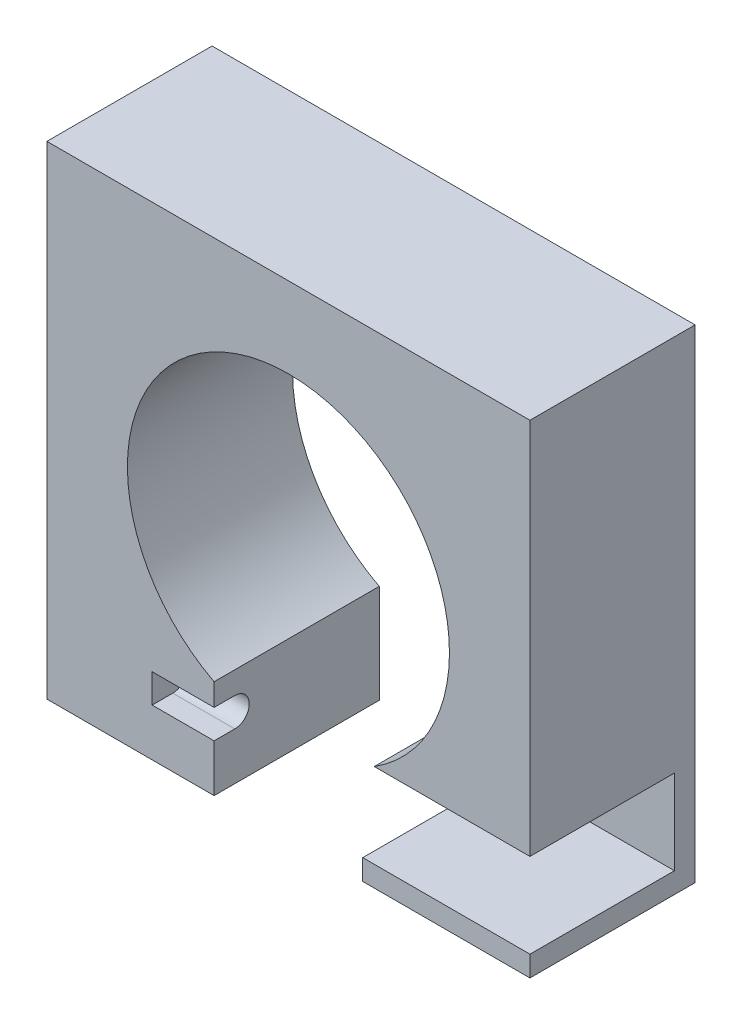
SolidWorks part; units mm, degrees
ref_plane "前基準面" through (0, 0, 0) normal (0, 0, 1) x (1, 0, 0)
ref_plane "上基準面" through (0, 0, 0) normal (0, 1, 0) x (1, 0, 0)
ref_plane "右基準面" through (0, 0, 0) normal (1, 0, 0) x (0, 0, -1)
sketch "草圖1" plane through (0, 0, 0) normal (0, 0, 1) x (1, 0, 0)
  line L1 (-53.8511, 32.0486) -> (63.1489, 32.0486)
  line L2 (-53.8511, 32.0486) -> (-53.8511, -84.9514)
  line L3 (-53.8511, -84.9514) -> (63.1489, -84.9514)
  line L4 (63.1489, 32.0486) -> (63.1489, -84.9514)
  circle A0 centre (4.6489, -26.4514) radius 39
  dimension "D1" = 78
  dimension "D3" = 58.5
  dimension "D4" = 117
  dimension "D5" = 58.5
  dimension "D2" = 117
extrude "填料-伸長1" add sketch "草圖1" along normal blind 40
sketch "草圖2" plane through (0, -84.9514, 0) normal (0, -1, 0) x (1, 0, 0)
  line L0 (-53.8511, 40) -> (63.1489, 40) construction
  line L1 (-13.3511, 40) -> (22.6489, 40)
  line L2 (-13.3511, 40) -> (-13.3511, 0)
  line L3 (-13.3511, 0) -> (22.6489, 0)
  line L4 (22.6489, 40) -> (22.6489, 0)
  line L5 (-53.8511, 0) -> (63.1489, 0) construction
  line L7 (63.1489, 40) -> (63.1489, 0) construction
  dimension "D1" = 36
  dimension "D2" = 40.5
extrude "除料-伸長1" cut sketch "草圖2" against normal up to next
sketch "草圖7" plane through (0, 0, 40) normal (0, 0, 1) x (1, 0, 0)
  line L0 (22.6489, -84.9514) -> (63.1489, -84.9514) construction
  line L1 (22.6489, -59.4514) -> (32.2989, -59.4514)
  line L2 (22.6489, -59.4514) -> (22.6489, -79.9514)
  line L3 (22.6489, -79.9514) -> (32.2989, -79.9514)
  line L4 (32.2989, -59.4514) -> (32.2989, -79.9514)
  line L6 (22.6489, -61.0491) -> (22.6489, -84.9514) construction
  dimension "D1" = 20.5
  dimension "D2" = 5
  dimension "D3" = 9.65
extrude "除料-伸長4" cut sketch "草圖7" against normal blind 40
sketch "草圖8" plane through (-13.3511, 0, 0) normal (1, 0, 0) x (0, 0, -1)
  line L0 (0, -61.0491) -> (0, -84.9514) construction
  line L1 (-40, -61.0491) -> (-40, -84.9514) construction
  line L2 (-40, -73.4514) -> (-35, -73.4514)
  line L3 (-40, -73.4514) -> (-40, -66.4514)
  line L4 (-40, -66.4514) -> (-35, -66.4514)
  line L5 (-35, -73.4514) -> (-35, -66.4514)
  line L6 (-40, -84.9514) -> (0, -84.9514) construction
  line L7 (-40, -61.0491) -> (0, -61.0491) construction
  circle A0 centre (-35, -69.9514) radius 3.5
  line M3 (-40, -61.0491) -> (-40, -84.9514)
  dimension "D1" = 7
  dimension "D2" = 35
  dimension "D3" = 7
  dimension "D4" = 11.5
extrude "除料-伸長5" cut sketch "草圖8" against normal blind 15 contours A0 L4 L2 M3 | L5 A0 | L5 A0
sketch "草圖9" plane through (0, 0, 40) normal (0, 0, 1) x (1, 0, 0)
  line L1 (32.2989, -59.4514) -> (63.2989, -59.4514)
  line L2 (32.2989, -59.4514) -> (32.2989, -79.9514)
  line L3 (32.2989, -79.9514) -> (63.2989, -79.9514)
  line L4 (63.2989, -59.4514) -> (63.2989, -79.9514)
  dimension "D1" = 31
  dimension "D2" = 20.5
extrude "除料-伸長6" cut sketch "草圖9" against normal blind 35
